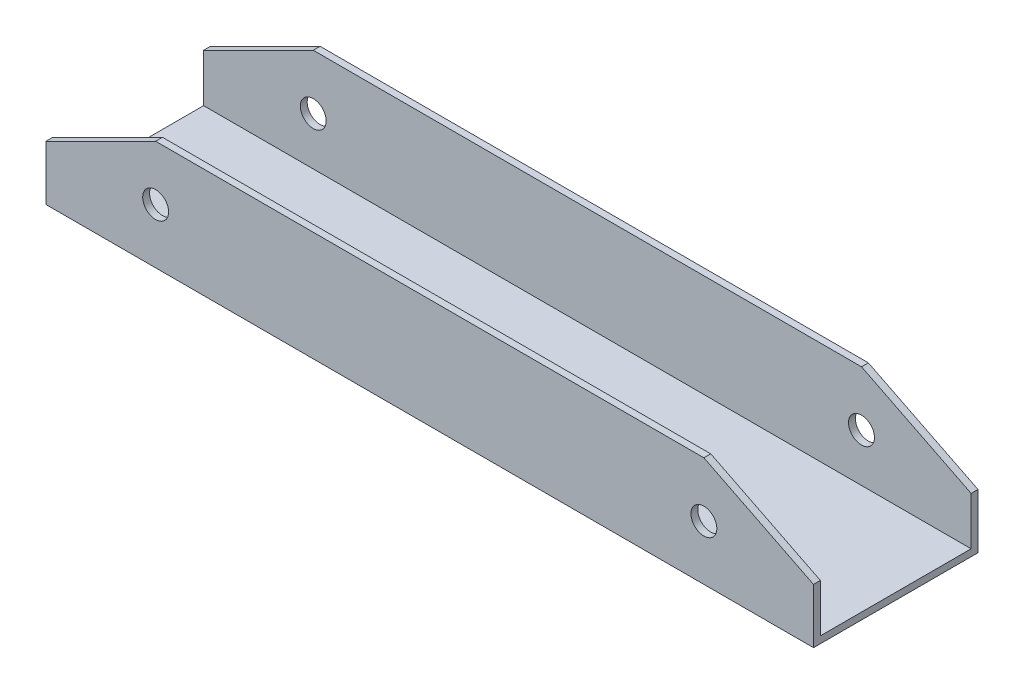
SolidWorks part; units mm, degrees
material "6061-T6 (SS)"
ref_plane "Front Plane" through (0, 0, 0) normal (0, 0, 1) x (1, 0, 0)
ref_plane "Top Plane" through (0, 0, 0) normal (0, 1, 0) x (1, 0, 0)
ref_plane "Right Plane" through (0, 0, 0) normal (1, 0, 0) x (0, 0, -1)
sketch "Sketch2" plane through (0, 0, 0) normal (1, 0, 0) x (0, 0, -1)
  line L1 (0, 0) -> (38.1, 0)
  line L2 (0, 0) -> (0, 38.1)
  line L3 (0, 38.1) -> (38.1, 38.1)
  line L4 (38.1, 0) -> (38.1, 38.1)
  line L5 (1.5875, 1.5875) -> (36.5125, 1.5875)
  line L6 (1.5875, 1.5875) -> (1.5875, 36.5125)
  line L7 (1.5875, 36.5125) -> (36.5125, 36.5125)
  line L8 (36.5125, 1.5875) -> (36.5125, 36.5125)
  dimension "D1" = 38.1
  dimension "D2" = 38.1
  dimension "D3" = 1.5875
  dimension "D4" = 1.5875
  dimension "D5" = 1.5875
  dimension "D6" = 1.5875
extrude "Boss-Extrude1" add sketch "Sketch2" along normal blind 228.6
sketch "Sketch3" plane through (0, 0, 0) normal (0, 0, 1) x (1, 0, 0)
  line L0 (25.4, 12.7) -> (152.4, 12.7) construction
  line L1 (228.6, 0) -> (0, 0) construction
  line L3 (0, 38.1) -> (0, 0) construction
  line L4 (0, 12.7) -> (25.4, 25.4)
  line L5 (25.4, 25.4) -> (152.4, 25.4)
  line L6 (152.4, 25.4) -> (177.8, 12.7)
  line L7 (177.8, 12.7) -> (177.8, 0)
  line L10 (0, 12.7) -> (0, 38.1)
  line L11 (0, 38.1) -> (228.6, 38.1)
  line L12 (228.6, 38.1) -> (228.6, 0)
  line L13 (228.6, 0) -> (177.8, 0)
  circle A0 centre (25.4, 12.7) radius 3
  circle A1 centre (152.4, 12.7) radius 3
  dimension "D6" = 6
  dimension "D7" = 6
  dimension "D1" = 127
  dimension "D2" = 12.7
  dimension "D3" = 25.4
  dimension "D4" = 25.4
  dimension "D5" = 25.4
extrude "Cut-Extrude1" cut sketch "Sketch3" against normal blind 228.6
